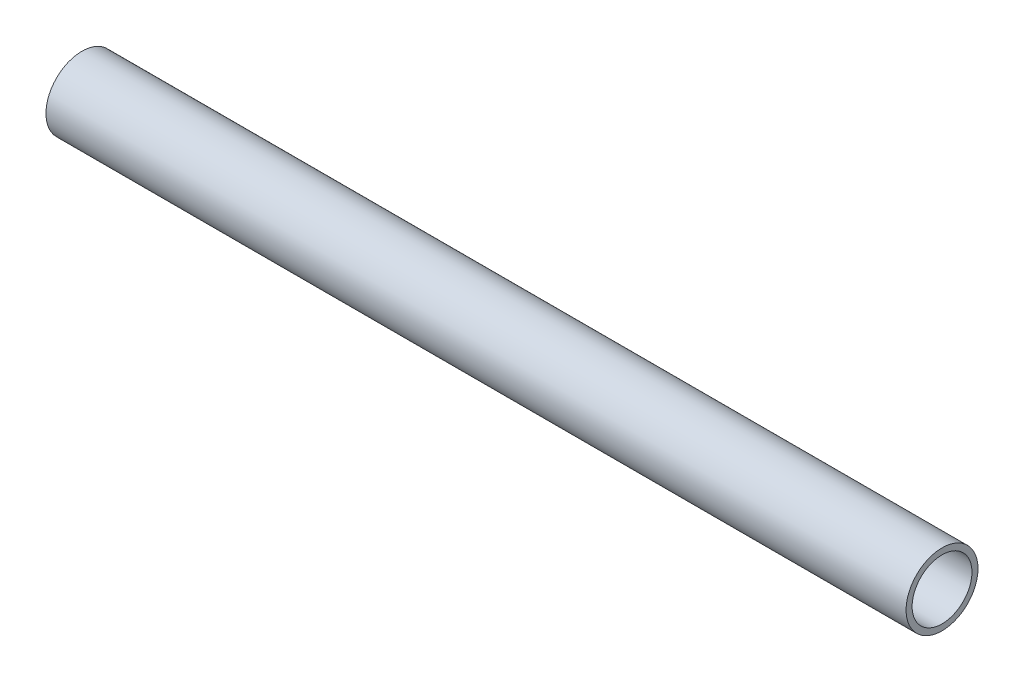
SolidWorks part; units mm, degrees
ref_plane "Front Plane" through (0, 0, 0) normal (0, 0, 1) x (1, 0, 0)
ref_plane "Top Plane" through (0, 0, 0) normal (0, 1, 0) x (1, 0, 0)
ref_plane "Right Plane" through (0, 0, 0) normal (1, 0, 0) x (0, 0, -1)
sketch "Sketch1" plane through (0, 0, 0) normal (0, 0, 1) x (1, 0, 0)
  line L0 (-279.8717, 1290.6663) -> (-128.0028, 1290.6663)
other "Pipe 0.5 SCH 40(1)"
ref_plane "Plane1" through (-279.8717, 1290.6663, 0) normal (1, 0, 0) x (0, 1, 0)
sketch "Sketch11" plane through (-279.8717, 1290.6663, 0) normal (1, 0, 0) x (0, 1, 0)
  circle A0 centre (0, 0) radius 5.2832
  circle A1 centre (0, 0) radius 6.35
  point P5 (0, 0)
  dimension "In_dia" = 10.5664
  dimension "Out_dia" = 12.7
